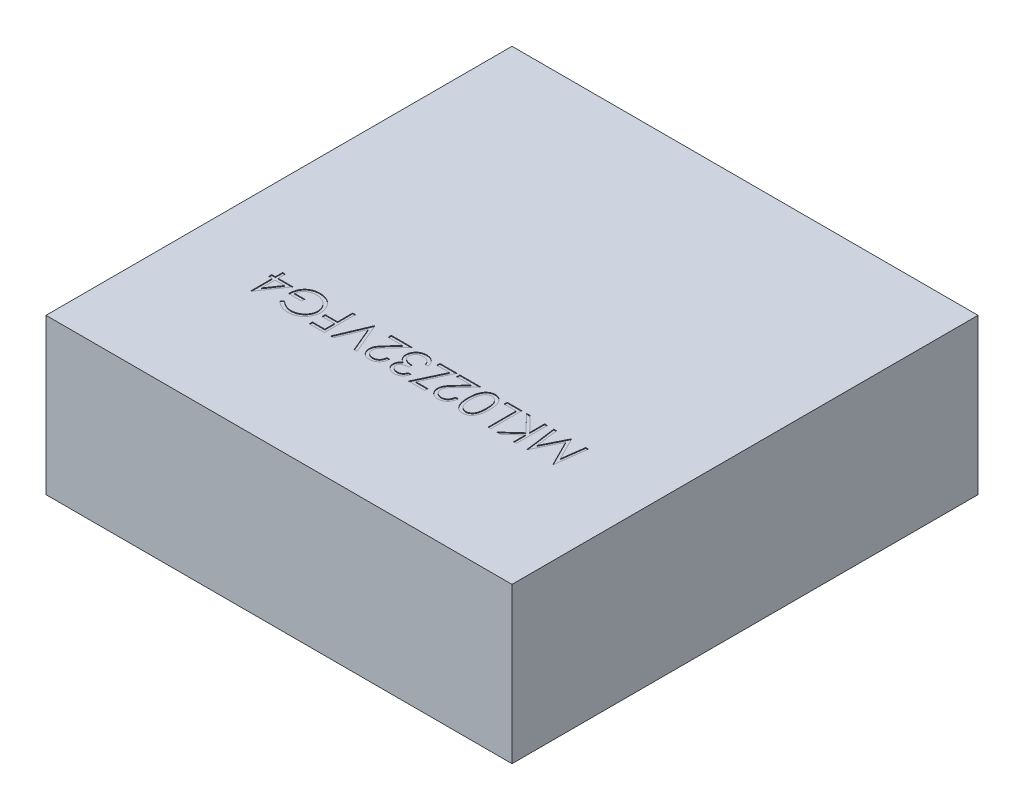
SolidWorks part; units mm, degrees
ref_plane "Front Plane" through (0, 0, 0) normal (0, 0, 1) x (1, 0, 0)
ref_plane "Top Plane" through (0, 0, 0) normal (0, 1, 0) x (1, 0, 0)
ref_plane "Right Plane" through (0, 0, 0) normal (1, 0, 0) x (0, 0, -1)
sketch "BaseS" plane through (0, 0, 0) normal (0, 1, 0) x (1, 0, 0)
  line L1 (-1.5, 1.5) -> (1.5, 1.5)
  line L2 (-1.5, 1.5) -> (-1.5, -1.5)
  line L3 (-1.5, -1.5) -> (1.5, -1.5)
  line L4 (1.5, 1.5) -> (1.5, -1.5)
  line L5 (-1.5, 1.5) -> (1.5, -1.5) construction
  line L6 (-1.5, -1.5) -> (1.5, 1.5) construction
  point P0 (0, 0)
  dimension "Dim" = 3
extrude "Base" add sketch "BaseS" along normal blind 1
sketch "PartNumberS" plane through (0, 1, 0) normal (0, 1, 0) x (1, 0, 0)
  line L0 (1.5, -0.5) -> (-1.5, -0.5) construction
  line L1 (1.5, -1.5) -> (1.5, 1.5) construction
  line L2 (-1.5, 1.5) -> (-1.5, -1.5) construction
  line L3 (-1.5, -1.5) -> (1.5, -1.5) construction
  text T0 "MKL02Z32VFG4" font "Century Gothic" height 0.2
  dimension "YDim" = 1
extrude "PartNumber" cut sketch "PartNumberS" against normal blind 0.005
